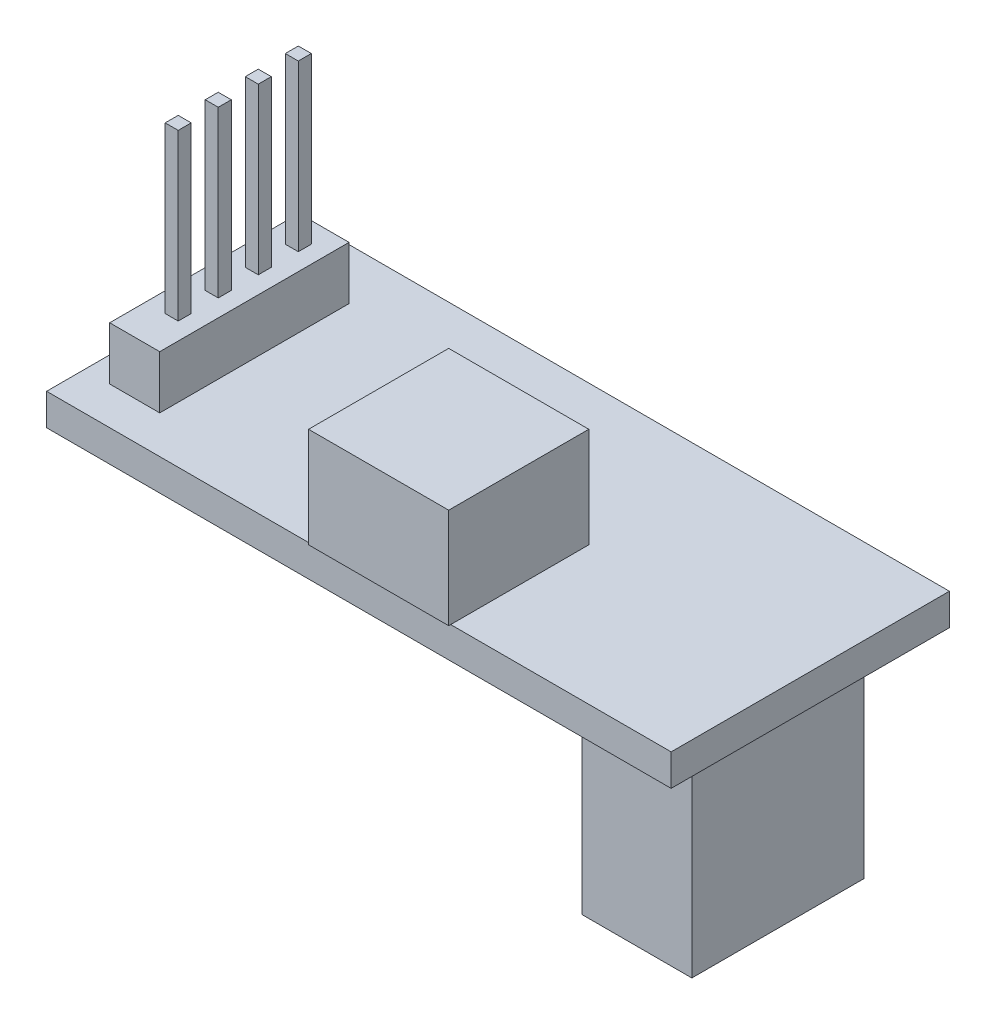
SolidWorks part; units mm, degrees
ref_plane "Plano frontal" through (0, 0, 0) normal (0, 0, 1) x (1, 0, 0)
ref_plane "Plano superior" through (0, 0, 0) normal (0, 1, 0) x (1, 0, 0)
ref_plane "Plano direito" through (0, 0, 0) normal (1, 0, 0) x (0, 0, -1)
sketch "Esboço1" plane through (0, 0, 0) normal (0, 1, 0) x (1, 0, 0)
  line L1 (-15.6, -6.95) -> (15.6, -6.95)
  line L2 (-15.6, -6.95) -> (-15.6, 6.95)
  line L3 (-15.6, 6.95) -> (15.6, 6.95)
  line L4 (15.6, -6.95) -> (15.6, 6.95)
  line L5 (-15.6, -6.95) -> (15.6, 6.95) construction
  line L6 (-15.6, 6.95) -> (15.6, -6.95) construction
  point P0 (0, 0)
  dimension "D1" = 31.2
  dimension "D2" = 13.9
extrude "Ressalto-extrusão1" add sketch "Esboço1" along normal blind 1.58
sketch "Esboço2" plane through (0, 1.58, 0) normal (0, 1, 0) x (1, 0, 0)
  line L0 (-15.6, -6.95) -> (15.6, -6.95) construction
  line L1 (-2.4135, -6.95) -> (4.5865, -6.95)
  line L2 (-2.4135, -6.95) -> (-2.4135, -0.05)
  line L3 (-2.4135, -0.05) -> (4.5865, -0.05)
  line L4 (4.5865, -6.95) -> (4.5865, -0.05)
  line L6 (-2.4135, -6.95) -> (4.5865, -6.95)
  line L7 (-2.4135, -6.95) -> (-2.4135, -7.05)
  line L8 (-2.4135, -7.05) -> (4.5865, -7.05)
  line L9 (4.5865, -6.95) -> (4.5865, -7.05)
  line M6 (-15.6, -6.95) -> (15.6, -6.95)
  dimension "D1" = 7
  dimension "D2" = 6.9
  dimension "D3" = 0.1
extrude "Ressalto-extrusão2" add sketch "Esboço2" along normal blind 5 contours L4 L3 L2 M6 | L9 L7 L8 M6
sketch "Esboço3" plane through (0, 0, 0) normal (0, -1, 0) x (1, 0, 0)
  line L0 (12.9186, -5.3633) -> (14.3209, -3.9611)
  line L1 (14.3209, 4.6367) -> (8.8209, 4.6367) construction
  line L2 (14.3209, 4.6367) -> (14.3209, -5.3633) construction
  line L3 (14.3209, -5.3633) -> (8.8209, -5.3633) construction
  line L4 (8.8209, 4.6367) -> (8.8209, -5.3633) construction
  line L5 (14.3209, -3.9611) -> (14.3209, 4.6367)
  line L6 (14.3209, 4.6367) -> (8.8209, 4.6367)
  line L7 (8.8209, 4.6367) -> (8.8209, -3.9611)
  line L8 (8.8209, -3.9611) -> (9.8557, -5.3633)
  line L9 (9.8557, -5.3633) -> (12.9186, -5.3633)
  dimension "D1" = 5.5
  dimension "D2" = 10
extrude "Ressalto-extrusão3" add sketch "Esboço3" along normal blind 10.5
chamfer "Chanfro1" distance 0.5 angle 45 6 edges at (13.6197, -10.5, -4.6622) (11.3872, -10.5, -5.3633) (9.3383, -10.5, -4.6622) (8.8209, -10.5, 0.3378) (11.5709, -10.5, 4.6367) (14.3209, -10.5, 0.3378)
sketch "Esboço4" plane through (0, 1.58, 0) normal (0, 1, 0) x (1, 0, 0)
  line L1 (-14.3382, 4.3971) -> (-11.8382, 4.3971)
  line L2 (-14.3382, 4.3971) -> (-14.3382, -5.0601)
  line L3 (-14.3382, -5.0601) -> (-11.8382, -5.0601)
  line L4 (-11.8382, 4.3971) -> (-11.8382, -5.0601)
  dimension "D1" = 2.5
extrude "Ressalto-extrusão4" add sketch "Esboço4" along normal blind 2.65
sketch "Esboço5" plane through (0, 4.23, 0) normal (0, 1, 0) x (1, 0, 0)
  line L1 (-12.7009, 3.375) -> (-13.3509, 3.375)
  line L2 (-12.7009, 3.375) -> (-12.7009, 2.725)
  line L3 (-12.7009, 2.725) -> (-13.3509, 2.725)
  line L4 (-13.3509, 3.375) -> (-13.3509, 2.725)
  dimension "D1" = 0.65
  dimension "D2" = 0.65
extrude "Ressalto-extrusão5" add sketch "Esboço5" along normal blind 8.25
pattern_linear "Padrão linear1" count 4 spacing 2 along (0, 0, 1) of "Ressalto-extrusão5"
